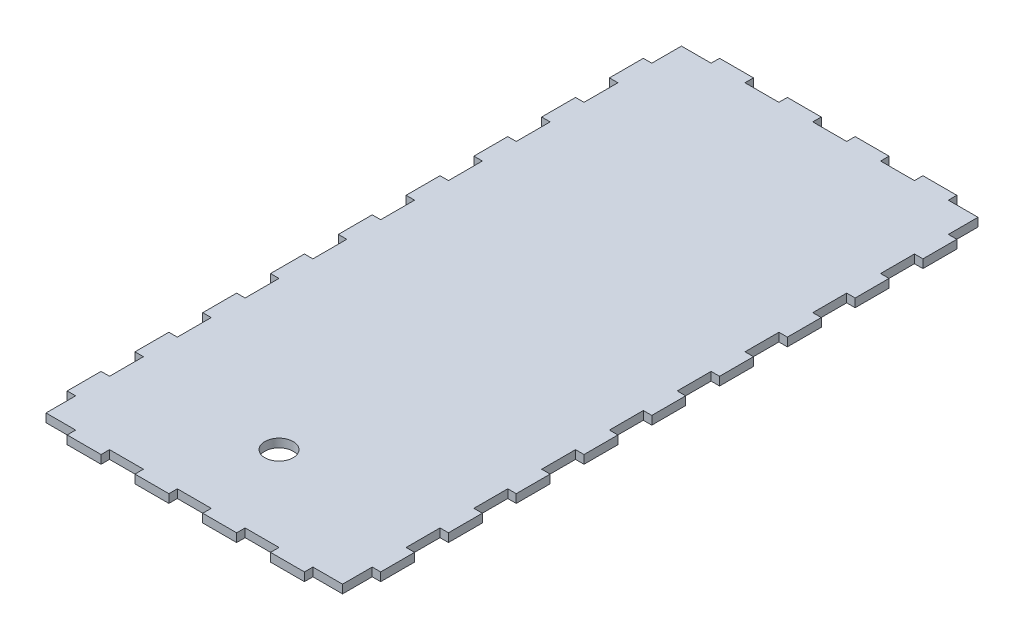
SolidWorks part; units mm, degrees
ref_plane "Front Plane" through (0, 0, 0) normal (0, 0, 1) x (1, 0, 0)
ref_plane "Top Plane" through (0, 0, 0) normal (0, 1, 0) x (1, 0, 0)
ref_plane "Right Plane" through (0, 0, 0) normal (1, 0, 0) x (0, 0, -1)
sketch "Sketch1" plane through (0, 0, 0) normal (0, 1, 0) x (1, 0, 0)
  line L1 (-105, -225) -> (105, -225)
  line L2 (-105, -225) -> (-105, 225)
  line L3 (-105, 225) -> (105, 225)
  line L4 (105, -225) -> (105, 225)
  line L5 (-105, -225) -> (105, 225) construction
  line L6 (-105, 225) -> (105, -225) construction
  circle A0 centre (0, -165) radius 10
  point P0 (0, 0)
  point P9 (0, -225)
  dimension "D1" = 20
  dimension "D2" = 60
extrude "Boss-Extrude1" add sketch "Sketch1" along normal blind 6
sketch "Sketch2" plane through (0, 6, 0) normal (0, 1, 0) x (1, 0, 0)
  line L0 (105, 225) -> (-105, 225) construction
  line L1 (-84, 225) -> (-60, 225)
  line L2 (-84, 225) -> (-84, 231)
  line L3 (-84, 231) -> (-60, 231)
  line L4 (-60, 225) -> (-60, 231)
  line L5 (-36, 225) -> (-36, 231)
  line L6 (-36, 225) -> (-12, 225)
  line L7 (-12, 225) -> (-12, 231)
  line L8 (-36, 231) -> (-12, 231)
  line L9 (12, 225) -> (12, 231)
  line L10 (12, 225) -> (36, 225)
  line L11 (36, 225) -> (36, 231)
  line L12 (12, 231) -> (36, 231)
  line L13 (60, 225) -> (60, 231)
  line L14 (60, 225) -> (84, 225)
  line L15 (84, 225) -> (84, 231)
  line L16 (60, 231) -> (84, 231)
  line L17 (-36, -231) -> (-36, -225)
  line L18 (-36, -231) -> (-12, -231)
  line L19 (-12, -231) -> (-12, -225)
  line L20 (-36, -225) -> (-12, -225)
  line L21 (12, -231) -> (12, -225)
  line L22 (12, -231) -> (36, -231)
  line L23 (36, -231) -> (36, -225)
  line L24 (12, -225) -> (36, -225)
  line L25 (60, -231) -> (60, -225)
  line L26 (60, -231) -> (84, -231)
  line L27 (84, -231) -> (84, -225)
  line L28 (60, -225) -> (84, -225)
  line L29 (-84, -231) -> (-84, -225)
  line L30 (-84, -231) -> (-60, -231)
  line L31 (-60, -231) -> (-60, -225)
  line L32 (-84, -225) -> (-60, -225)
  line L33 (-84, 225) -> (-84, -231) construction
  line L34 (-12, 225) -> (12, 225)
  line L35 (-12, -225) -> (12, -225)
  line L38 (105, -225) -> (105, 225) construction
  point P6 (0, 225)
  point P7 (-72, 225)
  point P8 (0, -225)
  point P39 (0, 0)
  point P40 (0, 0)
  point P41 (0, 0)
  point P42 (0, 0)
  point P43 (0, 0)
  point P44 (0, 0)
  point P45 (0, 0)
  point P46 (0, 0)
  point P47 (0, 0)
  point P48 (0, 0)
  dimension "D1" = 6
  dimension "D2" = 24
  dimension "D5" = 456
  dimension "D6" = 24
  dimension "D7" = 450
  dimension "D3" = 4
  dimension "D4" = 2
sketch "Sketch3" plane through (0, 6, 0) normal (0, 1, 0) x (1, 0, 0)
  line L0 (-105, 225) -> (-105, -225) construction
  line L1 (-105, 204) -> (-111, 204)
  line L2 (-105, 204) -> (-105, 180)
  line L3 (-105, 180) -> (-111, 180)
  line L4 (-111, 204) -> (-111, 180)
  line L5 (111, 204) -> (111, 180)
  line L6 (111, 204) -> (105, 204)
  line L7 (105, 204) -> (105, 180)
  line L8 (111, 180) -> (105, 180)
  line L9 (111, 156) -> (111, 132)
  line L10 (111, 156) -> (105, 156)
  line L11 (105, 156) -> (105, 132)
  line L12 (111, 132) -> (105, 132)
  line L13 (111, 108) -> (111, 84)
  line L14 (111, 108) -> (105, 108)
  line L15 (105, 108) -> (105, 84)
  line L16 (111, 84) -> (105, 84)
  line L17 (111, 60) -> (111, 36)
  line L18 (111, 60) -> (105, 60)
  line L19 (105, 60) -> (105, 36)
  line L20 (111, 36) -> (105, 36)
  line L21 (111, 12) -> (111, -12)
  line L22 (111, 12) -> (105, 12)
  line L23 (105, 12) -> (105, -12)
  line L24 (111, -12) -> (105, -12)
  line L25 (111, -36) -> (111, -60)
  line L26 (111, -36) -> (105, -36)
  line L27 (105, -36) -> (105, -60)
  line L28 (111, -60) -> (105, -60)
  line L29 (111, -84) -> (111, -108)
  line L30 (111, -84) -> (105, -84)
  line L31 (105, -84) -> (105, -108)
  line L32 (111, -108) -> (105, -108)
  line L33 (111, -132) -> (111, -156)
  line L34 (111, -132) -> (105, -132)
  line L35 (105, -132) -> (105, -156)
  line L36 (111, -156) -> (105, -156)
  line L37 (111, -180) -> (111, -204)
  line L38 (111, -180) -> (105, -180)
  line L39 (105, -180) -> (105, -204)
  line L40 (111, -204) -> (105, -204)
  line L41 (-105, 156) -> (-105, 132)
  line L42 (-105, 156) -> (-111, 156)
  line L43 (-111, 156) -> (-111, 132)
  line L44 (-105, 132) -> (-111, 132)
  line L45 (-105, 108) -> (-105, 84)
  line L46 (-105, 108) -> (-111, 108)
  line L47 (-111, 108) -> (-111, 84)
  line L48 (-105, 84) -> (-111, 84)
  line L49 (-105, 60) -> (-105, 36)
  line L50 (-105, 60) -> (-111, 60)
  line L51 (-111, 60) -> (-111, 36)
  line L52 (-105, 36) -> (-111, 36)
  line L53 (-105, 12) -> (-105, -12)
  line L54 (-105, 12) -> (-111, 12)
  line L55 (-111, 12) -> (-111, -12)
  line L56 (-105, -12) -> (-111, -12)
  line L57 (-105, -36) -> (-105, -60)
  line L58 (-105, -36) -> (-111, -36)
  line L59 (-111, -36) -> (-111, -60)
  line L60 (-105, -60) -> (-111, -60)
  line L61 (-105, -84) -> (-105, -108)
  line L62 (-105, -84) -> (-111, -84)
  line L63 (-111, -84) -> (-111, -108)
  line L64 (-105, -108) -> (-111, -108)
  line L65 (-105, -132) -> (-105, -156)
  line L66 (-105, -132) -> (-111, -132)
  line L67 (-111, -132) -> (-111, -156)
  line L68 (-105, -156) -> (-111, -156)
  line L69 (-105, -180) -> (-105, -204)
  line L70 (-105, -180) -> (-111, -180)
  line L71 (-111, -180) -> (-111, -204)
  line L72 (-105, -204) -> (-111, -204)
  point P7 (-105, 0)
  point P8 (0, 0)
  point P76 (0, 0)
  dimension "D1" = 6
  dimension "D2" = 24
  dimension "D3" = 2
  dimension "D4" = 9
extrude "Boss-Extrude3" add sketch "Sketch3" against normal blind 6
extrude "Boss-Extrude4" add sketch "Sketch2" against normal blind 6 contours L1 L4 L3 L2 | L8 L5 L6 L7 | L12 L9 L10 L11 | L16 L13 L14 L15 | L32 L29 L30 L31 | L20 L17 L18 L19 | L24 L21 L22 L23 | L28 L27 L26 L25
